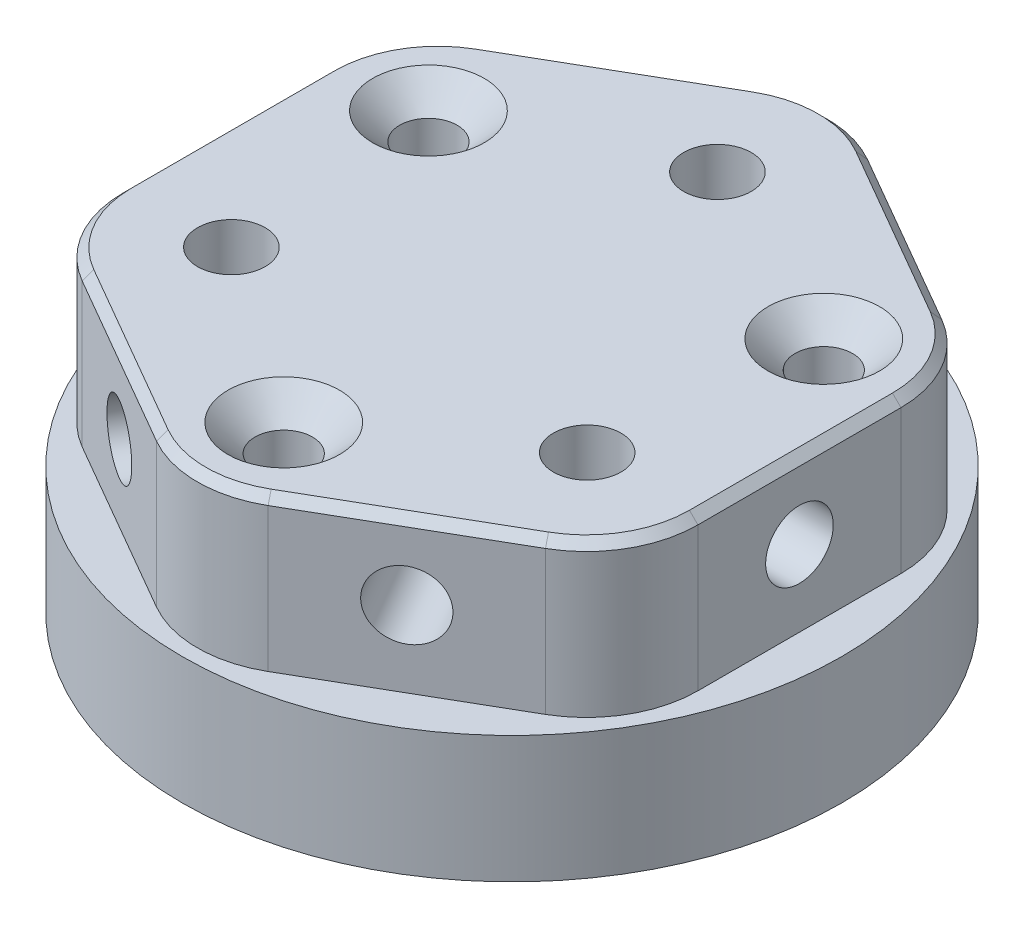
SolidWorks part; units mm, degrees
material "6061 合金"
ref_plane "前视基准面" through (0, 0, 0) normal (0, 0, 1) x (1, 0, 0)
ref_plane "上视基准面" through (0, 0, 0) normal (0, 1, 0) x (1, 0, 0)
ref_plane "右视基准面" through (0, 0, 0) normal (1, 0, 0) x (0, 0, -1)
sketch "草图9" plane through (0, 0, 0) normal (0, 1, 0) x (1, 0, 0)
  line L1 (0, 12.15) -> (-10.5222, -6.075) construction
  line L2 (-10.5222, -6.075) -> (10.5222, -6.075) construction
  line L3 (10.5222, -6.075) -> (0, 12.15) construction
  line L4 (0, -13.5) -> (11.6913, 6.75) construction
  line L5 (11.6913, 6.75) -> (-11.6913, 6.75) construction
  line L6 (-11.6913, 6.75) -> (0, -13.5) construction
  circle A0 centre (0, 0) radius 19.5
  circle A1 centre (0, 0) radius 13.5 construction
  circle A2 centre (0, 0) radius 12.15 construction
  circle A3 centre (0, 0) radius 6.075 construction
  circle A4 centre (0, 0) radius 6.75 construction
  circle A5 centre (0, 12.15) radius 2
  circle A6 centre (-10.5222, -6.075) radius 2
  circle A7 centre (10.5222, -6.075) radius 2
  circle A8 centre (-11.6913, 6.75) radius 1.5
  circle A9 centre (0, -13.5) radius 1.5
  circle A10 centre (11.6913, 6.75) radius 1.5
  dimension "D1" = 39
  dimension "D2" = 24.3
  dimension "D3" = 27
  dimension "D4" = 4
  dimension "D5" = 3
extrude "凸台-拉伸1" add sketch "草图9" along normal blind 7.5
sketch "草图13" plane through (0, 7.5, 0) normal (0, 1, 0) x (1, 0, 0)
  line L1 (-13.7, -11.7202) -> (-3.3, -17.7247)
  line L2 (3.3, -17.7247) -> (13.7, -11.7202)
  line L3 (17, -6.0044) -> (17, 6.0044)
  line L4 (13.7, 11.7202) -> (3.3, 17.7247)
  line L5 (-3.3, 17.7247) -> (-13.7, 11.7202)
  line L6 (-17, 6.0044) -> (-17, -6.0044)
  circle A0 centre (0, 0) radius 17 construction
  arc A2 (13.7, -11.7202) -> (17, -6.0044) centre (10.4, -6.0044) ccw
  arc A3 (17, 6.0044) -> (13.7, 11.7202) centre (10.4, 6.0044) ccw
  arc A4 (3.3, 17.7247) -> (-3.3, 17.7247) centre (0, 12.0089) ccw
  arc A5 (-13.7, 11.7202) -> (-17, 6.0044) centre (-10.4, 6.0044) ccw
  arc A6 (-13.7, -11.7202) -> (-17, -6.0044) centre (-10.4, -6.0044) cw
  arc A7 (-3.3, -17.7247) -> (3.3, -17.7247) centre (0, -12.0089) ccw
  dimension "D1" = 6.6
  dimension "D2" = 34
extrude "凸台-拉伸2" add sketch "草图13" along normal blind 12
sketch "草图15" plane through (-8.5, 0, -14.7224) normal (-0.5, 0, -0.866) x (-0.866, 0, 0.5)
  line L1 (0, 12) -> (0, 19.5) construction
  line L2 (-6.0044, 19.5) -> (6.0044, 19.5) construction
  circle A0 centre (0, 12) radius 2
  dimension "D2" = 4
  dimension "D1" = 7.5
extrude "切除-拉伸2" cut sketch "草图15" against normal through all both and the other way through all
sketch "草图16" plane through (8.5, 0, -14.7224) normal (0.5, 0, -0.866) x (-0.866, 0, -0.5)
  line L0 (0, 12) -> (0, 19.5) construction
  line L1 (-6.0044, 19.5) -> (6.0044, 19.5) construction
  circle A0 centre (0, 12) radius 2
  dimension "D2" = 4
  dimension "D1" = 7.5
extrude "切除-拉伸3" cut sketch "草图16" against normal through all both and the other way through all
sketch "草图17" plane through (17, 0, 0) normal (1, 0, 0) x (0, 0, -1)
  line L0 (0, 12) -> (0, 19.5) construction
  line L1 (-6.0044, 19.5) -> (6.0044, 19.5) construction
  circle A0 centre (0, 12) radius 2
  dimension "D1" = 4
  dimension "D2" = 7.5
extrude "切除-拉伸4" cut sketch "草图17" against normal through all both and the other way through all
sketch "草图18" plane through (0, 19.5, 0) normal (0, 1, 0) x (1, 0, 0)
  line L0 (-17, 6.0044) -> (-17, -6.0044) construction
  line L1 (-7, -4.0415) -> (0, -8.0829)
  line L2 (0, -8.0829) -> (7, -4.0415)
  line L3 (7, -4.0415) -> (7, 4.0415)
  line L4 (7, 4.0415) -> (0, 8.0829)
  line L5 (0, 8.0829) -> (-7, 4.0415)
  line L6 (-7, 4.0415) -> (-7, -4.0415)
  circle A0 centre (0, 0) radius 7 construction
  dimension "D1" = 10
extrude "凸台-拉伸3" add sketch "草图18" against normal up to surface (19.5 mm away) up to face at (0, 0, 19.5)
sketch "草图19" plane through (0, 7.5, 0) normal (0, -1, 0) x (1, 0, 0)
  circle A0 centre (-11.6913, -6.75) radius 1.5 construction
  circle A1 centre (-10.5222, 6.075) radius 2 construction
  circle A2 centre (0, 13.5) radius 1.5 construction
  circle A3 centre (10.5222, 6.075) radius 2 construction
  circle A4 centre (11.6913, -6.75) radius 1.5 construction
  circle A5 centre (0, -12.15) radius 2 construction
  circle A6 centre (-11.6913, -6.75) radius 1.5
  circle A7 centre (-10.5222, 6.075) radius 2
  circle A8 centre (0, 13.5) radius 1.5
  circle A9 centre (10.5222, 6.075) radius 2
  circle A10 centre (11.6913, -6.75) radius 1.5
  circle A11 centre (0, -12.15) radius 2
extrude "切除-拉伸5" cut sketch "草图19" against normal through all both and the other way through all
hole_wizard "打孔尺寸(%根据十字)槽沉头木螺钉的类型3" positions "草图20" profile "草图21" countersink size "M3" standard "GB" end condition through all
sketch "草图20" plane through (0, 19.5, 0) normal (0, 1, 0) x (1, 0, 0)
  point P0 (11.6913, 6.75)
  point P3 (0, -13.5)
  point P6 (-11.6913, 6.75)
sketch "草图21" plane through (11.6913, 19.5, -6.75) normal (1, 0, 0) x (0, 0, 1)
  line L0 (0, 0) -> (0, 19.5)
  line L1 (0, 19.5) -> (1.7, 19.5)
  line L2 (1.7, 19.5) -> (1.7, 1.6)
  line L3 (1.7, 1.6) -> (3.3, 0)
  line L5 (3.3, 0) -> (0, 0)
  line L6 (-1.7, 1.6) -> (-3.3, 0) construction
  line L11 (0, -6.35) -> (0, 107.95) construction
  dimension "通孔孔直径" = 3.4
  dimension "通孔孔深度" = 19.5
  dimension "近端锥形沉头孔直径" = 6.6
  dimension "近端锥形沉头孔角度" = 90
sketch "草图26" plane through (0, 19.5, 0) normal (0, 1, 0) x (1, 0, 0)
  line L6 (17, -6.0044) -> (17, 6.0044)
  line L7 (13.7, 11.7202) -> (3.3, 17.7247)
  line L8 (-3.3, 17.7247) -> (-13.7, 11.7202)
  line L9 (-17, 6.0044) -> (-17, -6.0044)
  line L10 (-13.7, -11.7202) -> (-3.3, -17.7247)
  line L11 (3.3, -17.7247) -> (13.7, -11.7202)
  line L12 (17, -6.0044) -> (17, 6.0044)
  line L13 (13.7, 11.7202) -> (3.3, 17.7247)
  line L14 (-3.3, 17.7247) -> (-13.7, 11.7202)
  line L15 (-17, 6.0044) -> (-17, -6.0044)
  line L16 (-13.7, -11.7202) -> (-3.3, -17.7247)
  line L17 (3.3, -17.7247) -> (13.7, -11.7202)
  arc A6 (13.7, -11.7202) -> (17, -6.0044) centre (10.4, -6.0044) ccw
  arc A7 (17, 6.0044) -> (13.7, 11.7202) centre (10.4, 6.0044) ccw
  arc A8 (3.3, 17.7247) -> (-3.3, 17.7247) centre (0, 12.0089) ccw
  arc A9 (-13.7, 11.7202) -> (-17, 6.0044) centre (-10.4, 6.0044) ccw
  arc A10 (-17, -6.0044) -> (-13.7, -11.7202) centre (-10.4, -6.0044) ccw
  arc A11 (-3.3, -17.7247) -> (3.3, -17.7247) centre (0, -12.0089) ccw
  arc A12 (13.7, -11.7202) -> (17, -6.0044) centre (10.4, -6.0044) ccw
  arc A13 (17, 6.0044) -> (13.7, 11.7202) centre (10.4, 6.0044) ccw
  arc A14 (3.3, 17.7247) -> (-3.3, 17.7247) centre (0, 12.0089) ccw
  arc A15 (-13.7, 11.7202) -> (-17, 6.0044) centre (-10.4, 6.0044) ccw
  arc A16 (-17, -6.0044) -> (-13.7, -11.7202) centre (-10.4, -6.0044) ccw
  arc A17 (-3.3, -17.7247) -> (3.3, -17.7247) centre (0, -12.0089) ccw
  dimension "D1" = 0
extrude "切除-拉伸6" cut sketch "草图26" against normal blind 3
chamfer "倒角2" distance 0.5 angle 45 12 edges at (8.5, 16.5, 14.7224) (16.1158, 16.5, 9.3044) (0, 16.5, 18.6089) (17, 16.5, 0) (-8.5, 16.5, 14.7224) (16.1158, 16.5, -9.3044) (-16.1158, 16.5, 9.3044) (8.5, 16.5, -14.7224) (-17, 16.5, 0) (0, 16.5, -18.6089) (-16.1158, 16.5, -9.3044) (-8.5, 16.5, -14.7224)
hole_wizard "打孔尺寸(%根据十字)槽沉头木螺钉的类型4" positions "草图27" profile "草图28" countersink size "M3" standard "GB" end condition through all
sketch "草图27" plane through (0, 16.5, 0) normal (0, 1, 0) x (1, 0, 0)
  point P0 (0, -13.5)
  point P3 (11.6913, 6.75)
  point P6 (-11.6913, 6.75)
sketch "草图28" plane through (0, 16.5, 13.5) normal (1, 0, 0) x (0, 0, 1)
  line L0 (0, 0) -> (0, 16.5)
  line L1 (0, 16.5) -> (1.6, 16.5)
  line L2 (1.6, 16.5) -> (1.6, 1.7)
  line L3 (1.6, 1.7) -> (3.3, 0)
  line L5 (3.3, 0) -> (0, 0)
  line L6 (-1.6, 1.7) -> (-3.3, 0) construction
  line L11 (0, -6.35) -> (0, 107.95) construction
  dimension "通孔孔直径" = 3.2
  dimension "通孔孔深度" = 16.5
  dimension "近端锥形沉头孔直径" = 6.6
  dimension "近端锥形沉头孔角度" = 90
